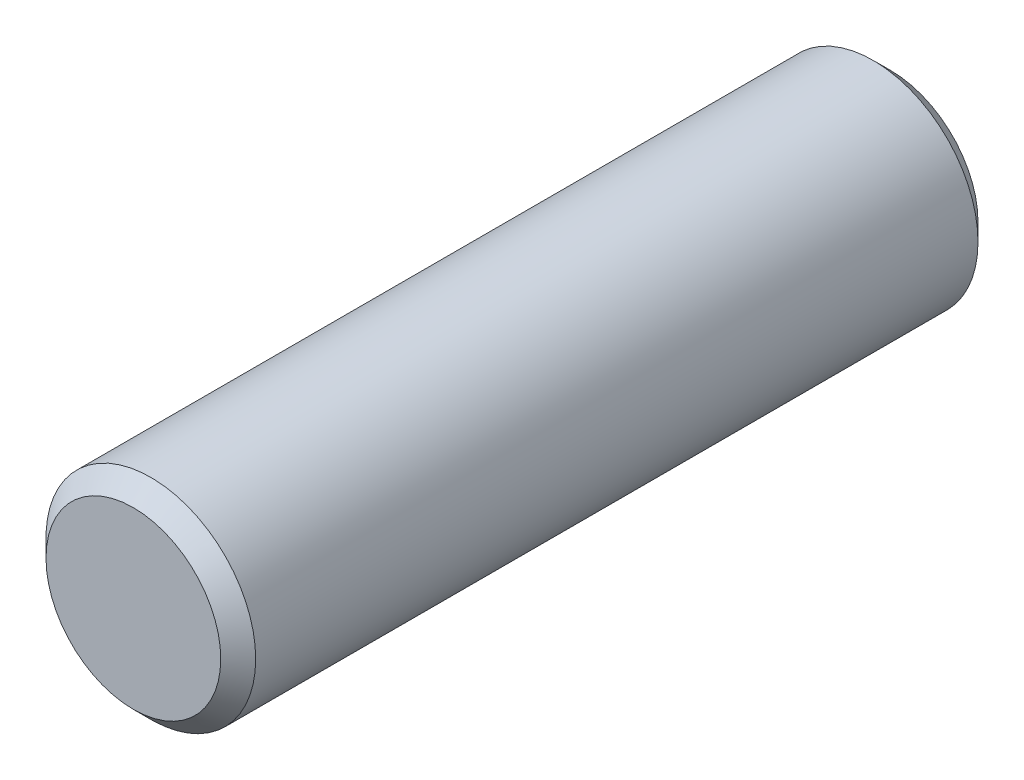
SolidWorks part; units mm, degrees
ref_plane "Plan de face" through (0, 0, 0) normal (0, 0, 1) x (1, 0, 0)
ref_plane "Plan de dessus" through (0, 0, 0) normal (0, 1, 0) x (1, 0, 0)
ref_plane "Plan de droite" through (0, 0, 0) normal (1, 0, 0) x (0, 0, -1)
sketch "Esquisse1" plane through (0, 0, 0) normal (0, 0, 1) x (1, 0, 0)
  circle A0 centre (0, 0) radius 9
  dimension "D1" = 18
extrude "Boss.-Extru.1" add sketch "Esquisse1" along normal mid plane 65
chamfer "Chanfrein1" distance 1.5 angle 45 2 edges at (9, 0, -32.5) (9, 0, 32.5)
